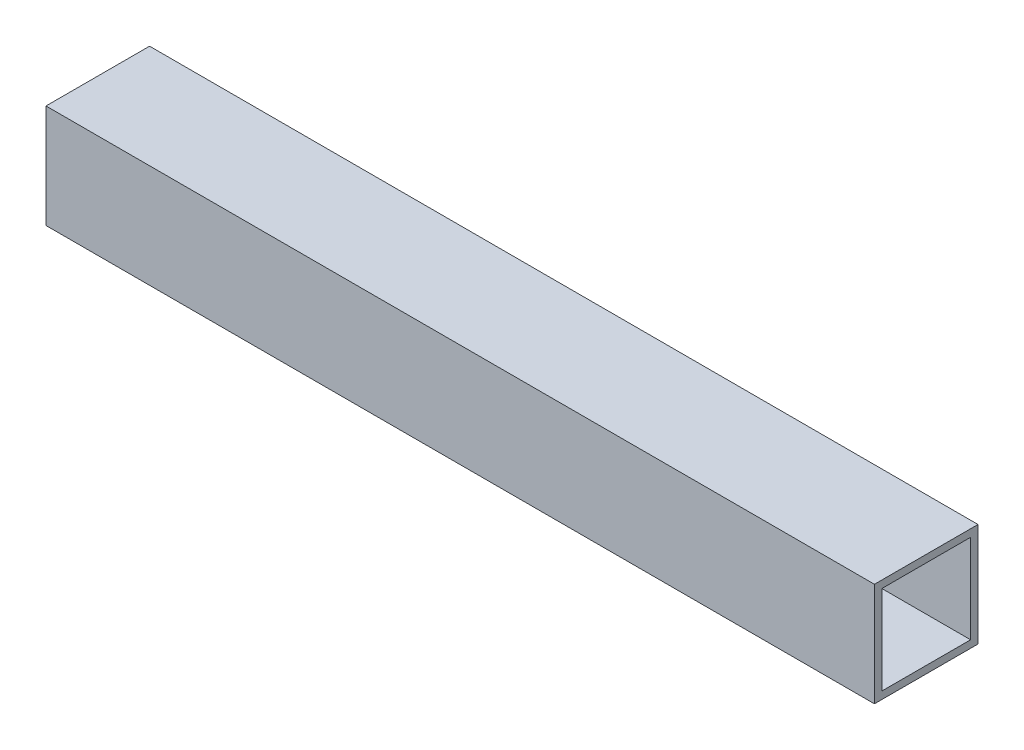
SolidWorks part; units mm, degrees
material "6061 Alloy"
ref_plane "Front Plane" through (0, 0, 0) normal (0, 0, 1) x (1, 0, 0)
ref_plane "Top Plane" through (0, 0, 0) normal (0, 1, 0) x (1, 0, 0)
ref_plane "Right Plane" through (0, 0, 0) normal (1, 0, 0) x (0, 0, -1)
sketch "Sketch1" plane through (0, 0, 0) normal (1, 0, 0) x (0, 0, -1)
  line L1 (0, 0) -> (44.45, 0)
  line L2 (0, 0) -> (0, 44.45)
  line L3 (0, 44.45) -> (44.45, 44.45)
  line L4 (44.45, 0) -> (44.45, 44.45)
  line L5 (41.275, 41.275) -> (3.175, 41.275)
  line L6 (41.275, 41.275) -> (41.275, 3.175)
  line L7 (41.275, 3.175) -> (3.175, 3.175)
  line L8 (3.175, 41.275) -> (3.175, 3.175)
  dimension "D1" = 44.45
  dimension "D2" = 38.1
  dimension "D3" = 44.45
  dimension "D4" = 3.175
  dimension "D5" = 3.175
  dimension "D6" = 38.1
extrude "Boss-Extrude1" add sketch "Sketch1" along normal blind 355.6
sketch "Sketch2" plane through (0, 0, 0) normal (0, 0, 1) x (1, 0, 0)
  line L0 (355.6, 44.45) -> (0, 44.45) construction
  line L1 (355.6, 44.45) -> (355.6, 0) construction
  circle A0 centre (330.2, 22.225) radius 2.4575
  circle A1 centre (279.4, 22.225) radius 2.4574
  dimension "D5" = 4.9149
  dimension "D1" = 22.225
  dimension "D2" = 22.225
  dimension "D3" = 50.8
  dimension "D4" = 25.4
